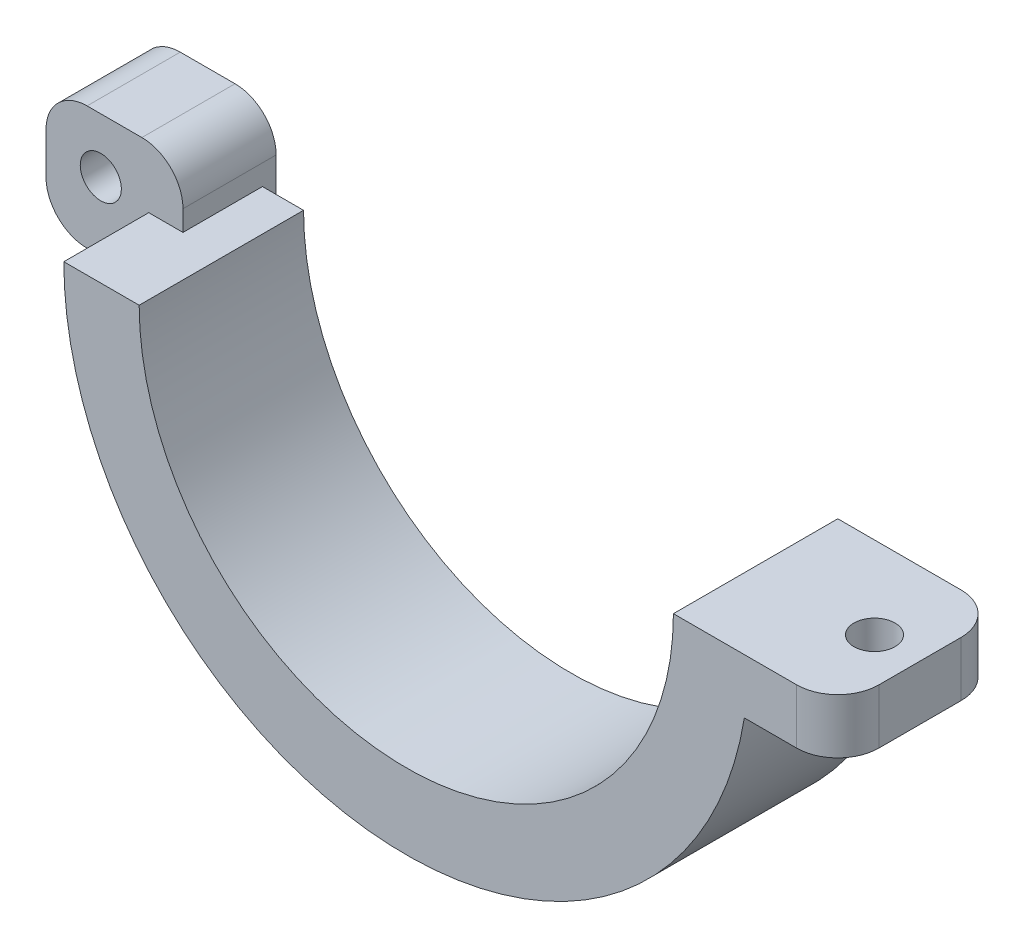
SolidWorks part; units mm, degrees
ref_plane "Front Plane" through (0, 0, 0) normal (0, 0, 1) x (1, 0, 0)
ref_plane "Top Plane" through (0, 0, 0) normal (0, 1, 0) x (1, 0, 0)
ref_plane "Right Plane" through (0, 0, 0) normal (1, 0, 0) x (0, 0, -1)
sketch "Sketch1" plane through (0, 0, 0) normal (0, 0, 1) x (1, 0, 0)
  line L0 (-25, 0) -> (25, 0)
  circle A0 centre (0, 0) radius 19.5
  circle A1 centre (0, 0) radius 25
  dimension "D2" = 39
  dimension "D3" = 0
  dimension "D4" = 50
  dimension "D1" = 0
  dimension "D5" = 25
  dimension "D6" = 25
  dimension "D7" = 0
extrude "Boss-Extrude8" add sketch "Sketch1" along normal blind 12
sketch "Sketch4" plane through (0, 0, 0) normal (0, 0, -1) x (-1, 0, 0)
  line L0 (-19.5, 0) -> (-25, 0) construction
  line L1 (-31.5, 0) -> (-23.5, 0)
  line L2 (-31.5, 0) -> (-31.5, -4)
  line L3 (-31.5, -4) -> (-23.5, -4)
  line L4 (-23.5, 0) -> (-23.5, -4)
  dimension "D1" = 4
  dimension "D2" = 0
  dimension "D3" = 4
  dimension "D4" = 8
extrude "Boss-Extrude10" add sketch "Sketch4" against normal blind 12
sketch "Sketch5" plane through (0, -4, 0) normal (0, -1, 0) x (1, 0, 0)
  line L0 (24.6779, 0) -> (24.6779, 12) construction
  line L1 (31.5, 0) -> (24.6779, 0) construction
  circle A0 centre (28.1779, 6) radius 1.5
  dimension "D1" = 3
  dimension "D2" = 3.5
  dimension "D3" = 6
extrude "Cut-Extrude2" cut sketch "Sketch5" against normal blind 12
sketch "Sketch6" plane through (0, 0, 0) normal (0, 0, -1) x (-1, 0, 0)
  line L0 (25, 0) -> (19.5, 0) construction
  line L1 (22.5, -4.5) -> (32.5, -4.5)
  line L2 (22.5, -4.5) -> (22.5, 4.5)
  line L3 (22.5, 4.5) -> (32.5, 4.5)
  line L4 (32.5, -4.5) -> (32.5, 4.5)
  dimension "D1" = 3
  dimension "D2" = 4.5
  dimension "D3" = 10
  dimension "D4" = 9
extrude "Boss-Extrude11" add sketch "Sketch6" against normal blind 5.8 and the other way blind 1
sketch "Sketch7" plane through (0, 0, -1) normal (0, 0, -1) x (-1, 0, 0)
  line L0 (32.5, 4.5) -> (22.5, 4.5) construction
  line L1 (32.5, -4.5) -> (32.5, 4.5) construction
  circle A0 centre (28.5, 0.5) radius 1.5
  dimension "D1" = 3
  dimension "D2" = 4
  dimension "D3" = 4
extrude "Cut-Extrude3" cut sketch "Sketch7" against normal blind 10
fillet "Fillet1" radius 3 1 edges at (-32.5, -4.5, 2.4)
fillet "Fillet3" radius 3 1 edges at (-32.5, 4.5, 2.4)
fillet "Fillet4" radius 3 1 edges at (-22.5, 4.5, 2.4)
fillet "Fillet5" radius 3 1 edges at (31.5, -2, 0)
fillet "Fillet6" radius 3 1 edges at (31.5, -2, 12)
